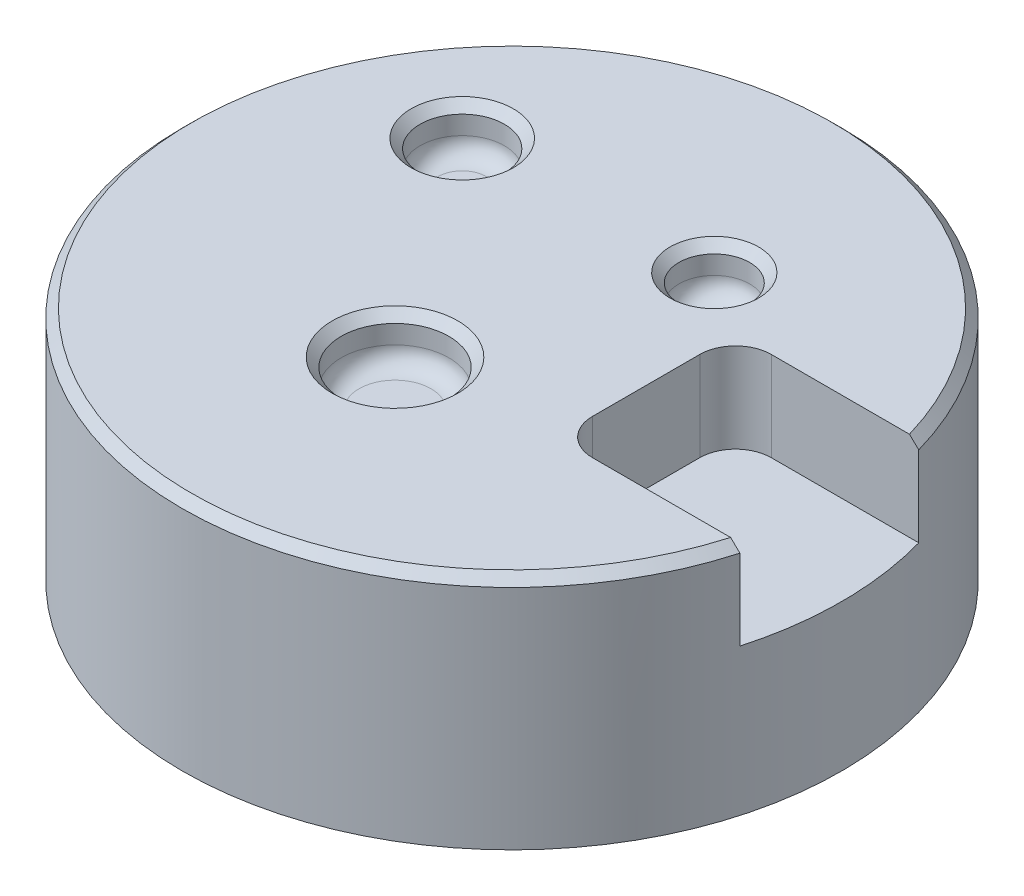
SolidWorks part; units mm, degrees
ref_plane "Front Plane" through (0, 0, 0) normal (0, 0, 1) x (1, 0, 0)
ref_plane "Top Plane" through (0, 0, 0) normal (0, 1, 0) x (1, 0, 0)
ref_plane "Right Plane" through (0, 0, 0) normal (1, 0, 0) x (0, 0, -1)
sketch "Sketch1" plane through (0, 0, 0) normal (0, 1, 0) x (1, 0, 0)
  circle A0 centre (0, 0) radius 36.8717
extrude "Boss-Extrude1" add sketch "Sketch1" along normal blind 26.416
sketch "Sketch2" plane through (0, 26.416, 0) normal (0, 1, 0) x (1, 0, 0)
  circle A0 centre (-19.2212, 13.6555) radius 4.7194
  circle A1 centre (7.8766, 14.7482) radius 3.9562
  circle A2 centre (-1.7864, -11.2952) radius 6.0255
extrude "Cut-Extrude1" cut sketch "Sketch2" against normal blind 5.08
sketch "Sketch3" plane through (0, 26.416, 0) normal (0, 1, 0) x (1, 0, 0)
  circle A0 centre (0, 0) radius 62.055
chamfer "Chamfer1" distance 1 angle 45 1 edges at (0, 26.416, 36.8717)
sketch "Sketch4" plane through (0, 26.416, 0) normal (0, 1, 0) x (1, 0, 0)
  line L1 (15, -10) -> (45, -10)
  line L2 (15, -10) -> (15, 10)
  line L3 (15, 10) -> (45, 10)
  line L4 (45, -10) -> (45, 10)
  line L5 (15, -10) -> (45, 10) construction
  line L6 (15, 10) -> (45, -10) construction
  circle A0 centre (0, 0) radius 36.8717 construction
  point P0 (30, 0)
  dimension "D1" = 20
  dimension "D2" = 10
  dimension "D3" = 30
  dimension "D4" = 30
extrude "Cut-Extrude2" cut sketch "Sketch4" against normal blind 10
fillet "Fillet1" radius 4 2 edges at (15, 21.416, 10) (15, 21.416, -10)
fillet "Fillet3" radius 2 3 edges at (-1.7864, 21.336, 17.3207) (7.8766, 21.336, -10.792) (-19.2212, 21.336, -8.9361)
chamfer "Chamfer3" distance 1 angle 45 3 edges at (-1.7864, 26.416, 17.3207) (7.8766, 26.416, -10.792) (-19.2212, 26.416, -8.9361)
